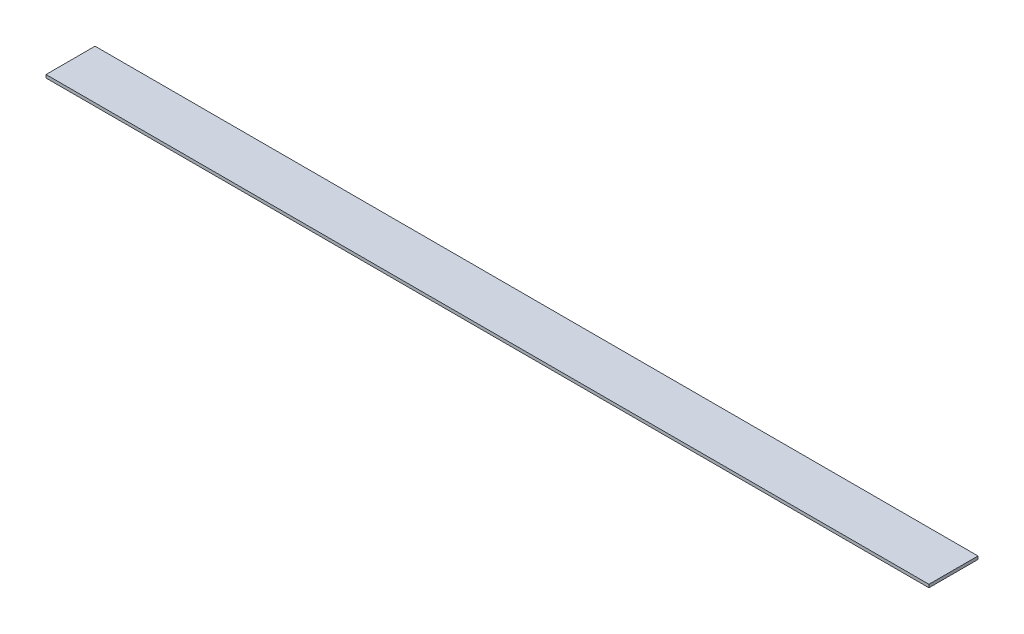
SolidWorks part; units mm, degrees
ref_plane "Front Plane" through (0, 0, 0) normal (0, 0, 1) x (1, 0, 0)
ref_plane "Top Plane" through (0, 0, 0) normal (0, 1, 0) x (1, 0, 0)
ref_plane "Right Plane" through (0, 0, 0) normal (1, 0, 0) x (0, 0, -1)
sketch "Sketch1" plane through (0, 0, 0) normal (0, 1, 0) x (1, 0, 0)
  line L1 (457.2, 25.4) -> (-457.2, 25.4)
  line L2 (457.2, 25.4) -> (457.2, -25.4)
  line L3 (457.2, -25.4) -> (-457.2, -25.4)
  line L4 (-457.2, 25.4) -> (-457.2, -25.4)
  line L5 (457.2, 25.4) -> (-457.2, -25.4) construction
  line L6 (457.2, -25.4) -> (-457.2, 25.4) construction
  point P1 (0, 0)
  dimension "D1" = 50.8
  dimension "D2" = 914.4
extrude "Boss-Extrude1" add sketch "Sketch1" along normal blind 3.175
